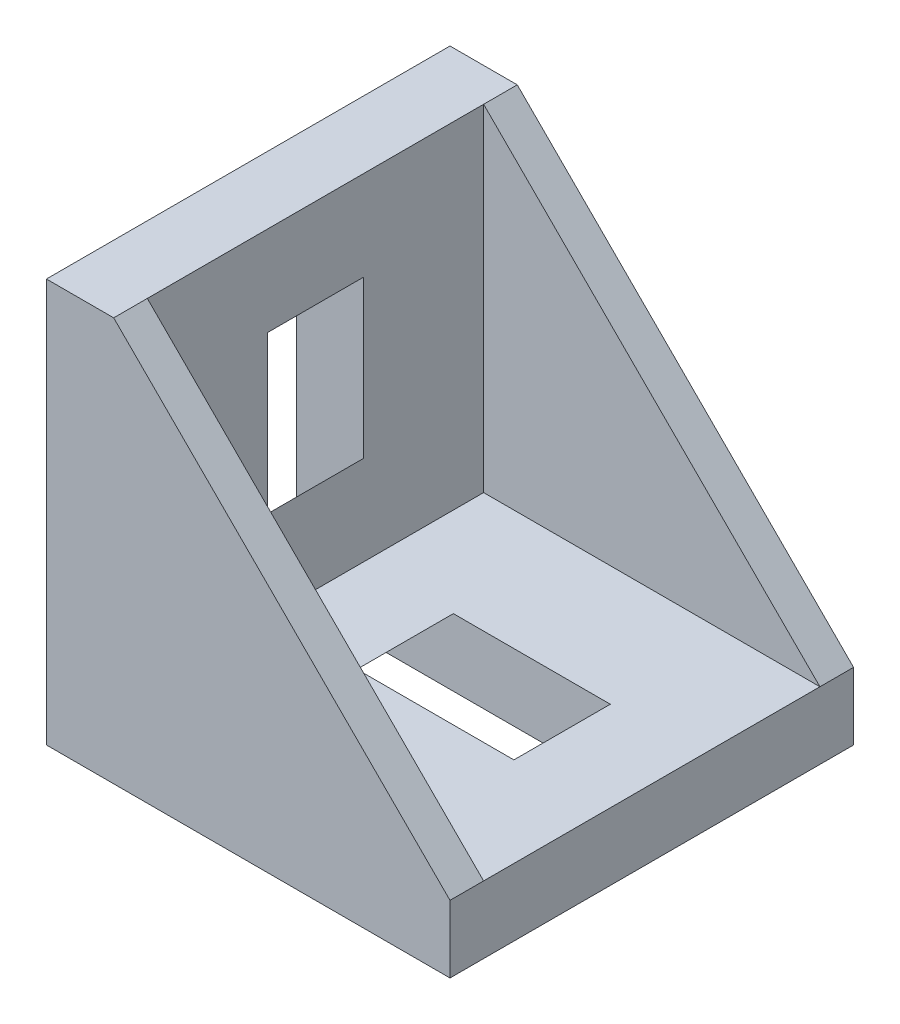
SolidWorks part; units mm, degrees
ref_plane "Front Plane" through (0, 0, 0) normal (0, 0, 1) x (1, 0, 0)
ref_plane "Top Plane" through (0, 0, 0) normal (0, 1, 0) x (1, 0, 0)
ref_plane "Right Plane" through (0, 0, 0) normal (1, 0, 0) x (0, 0, -1)
sketch "Sketch1" plane through (0, 0, 0) normal (0, 0, 1) x (1, 0, 0)
  line L0 (0, 0) -> (0, 18)
  line L1 (18, 3) -> (3, 18)
  line L4 (3, 18) -> (0, 18)
  line L5 (18, 0) -> (0, 0)
  line L7 (18, 3) -> (18, 0)
  dimension "D" = 3
  dimension "C" = 18
  dimension "B" = 18
extrude "Boss-Extrude1" add sketch "Sketch1" along normal mid plane 18
sketch "Sketch2" plane through (0, 0, 0) normal (0, 0, 1) x (1, 0, 0)
  line L0 (3, 18) -> (3, 3)
  line L1 (3, 3) -> (18, 3)
  line L2 (3, 18) -> (18, 3)
extrude "Cut-Extrude1" cut sketch "Sketch2" against normal mid plane 15
sketch "Sketch3" plane through (0, 0, 0) normal (0, 0, 1) x (1, 0, 0)
  line L0 (18, 3) -> (3, 18) construction
  line L1 (0, 14) -> (3, 14)
  line L2 (0, 14) -> (0, 4)
  line L3 (0, 4) -> (3, 7)
  line L4 (3, 14) -> (3, 7)
  line L5 (7, 3) -> (14, 3)
  line L6 (7, 3) -> (4, 0)
  line L7 (4, 0) -> (14, 0)
  line L8 (14, 3) -> (14, 0)
  line L9 (3, 18) -> (0, 18) construction
  line L10 (18, 0) -> (0, 0) construction
  line L11 (0, 0) -> (0, 18) construction
  line L12 (18, 0) -> (18, 3) construction
  dimension "D1" = 14
  dimension "D2" = 7
  dimension "D3" = 14
  dimension "D4" = 7
  dimension "D5" = 4
  dimension "D6" = 4
extrude "Cut-Extrude2" cut sketch "Sketch3" against normal mid plane 4.3
sketch "Sketch4" plane through (0, 0, 0) normal (0, 0, 1) x (1, 0, 0)
  line L0 (0, 18) -> (0, 0) construction
  line L1 (1.2115, 2.3429) -> (0, 1.2348) construction
  line L2 (1.5046, -1.8) -> (0.5112, -0.7909)
  line L3 (0, 3.5355) -> (-1.8, 1.5046)
  line L4 (-1.8, 1.5046) -> (-0.7909, 0.5112)
  line L5 (-0.7909, 0.5112) -> (0, 1.2348)
  line L6 (0, 1.2348) -> (0, 3.5355)
  line L7 (0.5112, -0.7909) -> (1.2348, 0)
  line L8 (0, 0) -> (0, 18) construction
  line L9 (-1.2955, 1.0079) -> (0, 2.3239) construction
  line L10 (1.2348, 0) -> (3.5355, 0)
  line L11 (3.5355, 0) -> (1.5046, -1.8)
  line L12 (0, 17.3) -> (0, 14.9992)
  line L13 (0, 14.9992) -> (-0.7909, 14.2757)
  line L14 (-0.7909, 14.2757) -> (-1.8, 15.269)
  line L15 (-1.8, 15.269) -> (0, 17.3)
  line L16 (-1.2955, 14.7724) -> (0, 16.0884) construction
  line L17 (0, 16.0884) -> (0.6057, 16.7037) construction
  line L18 (18, 3) -> (3, 18) construction
  line L19 (10.5, 10.5) -> (0, 0) construction
  line L20 (0, 17.3) -> (1.2115, 16.1074) construction
  line L21 (0, 14.9992) -> (1.2115, 16.1074) construction
  line L22 (0, 3.5355) -> (1.2115, 2.3429) construction
  line L23 (14.9992, 0) -> (14.2757, -0.7909)
  line L24 (0.6057, 2.9392) -> (0, 2.3239) construction
  line L25 (14.2757, -0.7909) -> (15.269, -1.8)
  line L26 (17.3, 0) -> (14.9992, 0)
  line L27 (15.269, -1.8) -> (17.3, 0)
  line L28 (-1.8, 1.5046) -> (-1.8, 15.269) construction
  dimension "D1" = 1.7
  dimension "D2" = 5
  dimension "D3" = 6
  dimension "D4" = 1.6001
  dimension "D5" = 0.7
  dimension "D6" = 0.1905
  dimension "D7" = 1.8
extrude "Boss-Extrude2" add sketch "Sketch4" along normal mid plane 5
